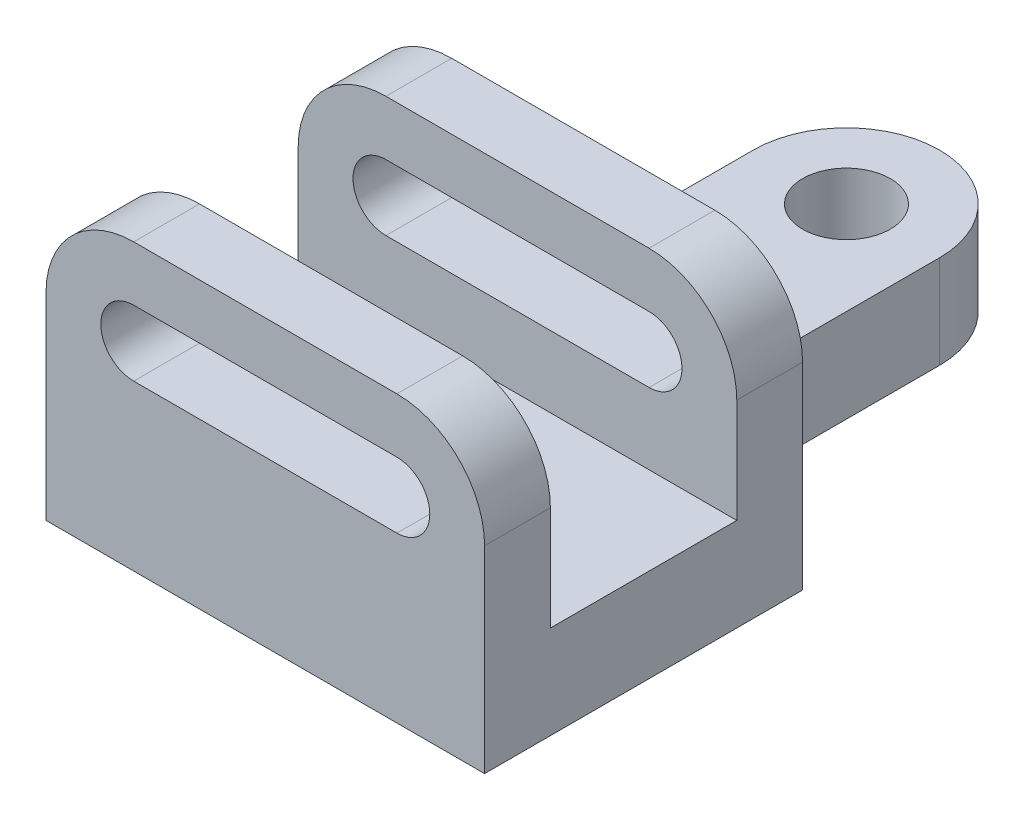
SolidWorks part; units mm, degrees
ref_plane "前基準面" through (0, 0, 0) normal (0, 0, 1) x (1, 0, 0)
ref_plane "上基準面" through (0, 0, 0) normal (0, 1, 0) x (1, 0, 0)
ref_plane "右基準面" through (0, 0, 0) normal (1, 0, 0) x (0, 0, -1)
sketch "草圖1" plane through (0, 0, 0) normal (0, 0, 1) x (1, 0, 0)
  line L0 (-24, 0) -> (24, 0) construction
  line L1 (-24, 6) -> (24, 6)
  line L2 (-24, -6) -> (24, -6)
  line L3 (-24, 16) -> (24, 16)
  line L4 (-40, 0) -> (-40, -36)
  line L5 (-40, -36) -> (40, -36)
  line L6 (40, -36) -> (40, 0)
  arc A0 (-24, 6) -> (-24, -6) centre (-24, 0) ccw
  arc A1 (24, -6) -> (24, 6) centre (24, 0) ccw
  arc A2 (-40, 0) -> (-24, 16) centre (-24, 0) cw
  arc A3 (40, 0) -> (24, 16) centre (24, 0) ccw
  point P3 (0, 0)
  dimension "D1" = 6
  dimension "D2" = 16
  dimension "D3" = 80
  dimension "D4" = 16
  dimension "D5" = 52
extrude "填料-伸長2" add sketch "草圖1" along normal mid plane 58
sketch "草圖3" plane through (0, 0, 0) normal (1, 0, 0) x (0, 0, -1)
  line L0 (-29, 16) -> (29, 16) construction
  line L1 (-17, 16) -> (17, 16)
  line L2 (-17, 16) -> (-17, -19)
  line L3 (-17, -19) -> (17, -19)
  line L4 (17, 16) -> (17, -19)
  line L5 (0, 16.9016) -> (0, -15.9322) construction
  line L6 (-29, -36) -> (29, -36) construction
  dimension "D1" = 34
  dimension "D2" = 17
extrude "除料-伸長1" cut sketch "草圖3" against normal through all both and the other way through all
sketch "草圖4" plane through (0, -36, 0) normal (0, -1, 0) x (1, 0, 0)
  line L0 (-17, -77) -> (-17, -45)
  line L3 (17, -77) -> (17, -45)
  line L4 (-33, -29) -> (33, -29)
  line L5 (0, 0) -> (0, -98.3211) construction
  line L6 (-40, -29) -> (40, -29) construction
  circle A0 centre (0, -77) radius 8
  arc A1 (-17, -77) -> (17, -77) centre (0, -77) ccw
  arc A2 (-17, -45) -> (-33, -29) centre (-33, -45) ccw
  arc A3 (33, -29) -> (17, -45) centre (33, -45) ccw
  dimension "D1" = 17
  dimension "16" = 16
  dimension "D2" = 16
  dimension "D3" = 16
  dimension "D4" = 48
extrude "填料-伸長3" add sketch "草圖4" against normal blind 17
